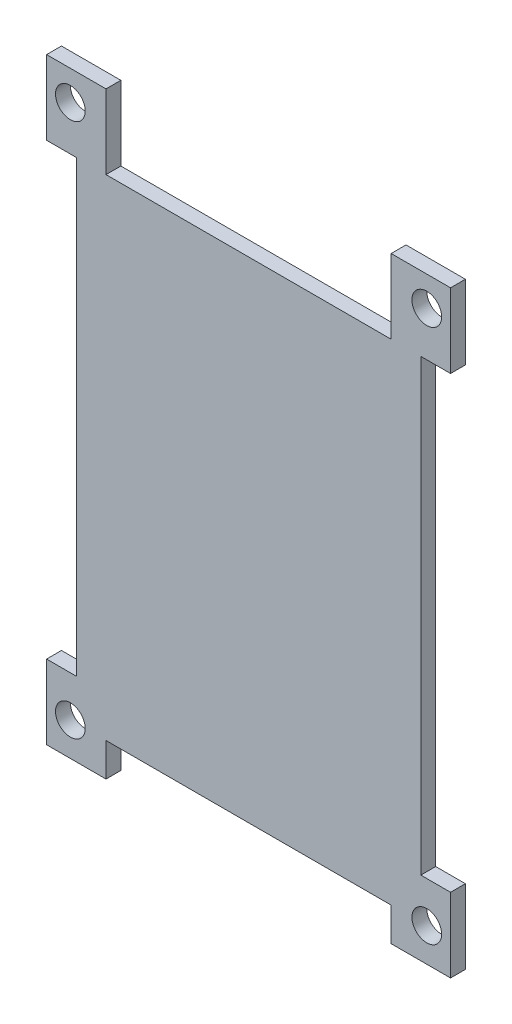
SolidWorks part; units mm, degrees
material "PVC 0.007 plastifié"
ref_plane "Face" through (0, 0, 0) normal (0, 0, 1) x (1, 0, 0)
ref_plane "Dessus" through (0, 0, 0) normal (0, 1, 0) x (1, 0, 0)
ref_plane "Droite" through (0, 0, 0) normal (1, 0, 0) x (0, 0, -1)
sketch "Esquisse1" plane through (0, 0, 0) normal (0, 0, 1) x (1, 0, 0)
  line L0 (0, 0) -> (33.0541, 0) construction
  line L1 (-19.2, 33) -> (19.2, 33)
  line L2 (-23.2, 33) -> (-23.2, -27.5)
  line L3 (19.2, -33) -> (-19.2, -33)
  line L4 (23.2, 33) -> (23.2, -27.5)
  line L5 (0, 0) -> (0, 31.1956) construction
  line L6 (19.2, 43) -> (19.2, 33)
  line L7 (-27.2, 43) -> (-19.2, 43)
  line L8 (-27.2, 43) -> (-27.2, 33)
  line L9 (-27.2, 33) -> (-23.2, 33)
  line L10 (-19.2, 43) -> (-19.2, 33)
  line L11 (19.2, -37.5) -> (27.2, -37.5)
  line L12 (27.2, 43) -> (27.2, 33)
  line L13 (27.2, 43) -> (19.2, 43)
  line L14 (27.2, -37.5) -> (27.2, -27.5)
  line L15 (27.2, -27.5) -> (23.2, -27.5)
  line L16 (-19.2, -37.5) -> (-27.2, -37.5)
  line L17 (-19.2, -37.5) -> (-19.2, -33)
  line L18 (-27.2, -37.5) -> (-27.2, -27.5)
  line L21 (19.2, -37.5) -> (19.2, -33)
  line L22 (-27.2, -27.5) -> (-23.2, -27.5)
  line L23 (23.2, 33) -> (27.2, 33)
  dimension "D1" = 46.4
  dimension "D2" = 66
  dimension "D3" = 8
  dimension "D4" = 4
  dimension "D5" = 10
  dimension "D6" = 4.5
  dimension "D7" = 10
  dimension "D8" = 8
  dimension "D9" = 8
  dimension "D10" = 4
  dimension "D11" = 27.5
extrude "Extrusion1" add sketch "Esquisse1" along normal blind 2
sketch "Esquisse2" plane through (0, 0, 2) normal (0, 0, 1) x (1, 0, 0)
  line L0 (0, 0) -> (0, 28.1312) construction
  line L3 (0, 0) -> (33.3419, 0) construction
  line L5 (-19.2, 43) -> (-27.2, 43) construction
  circle A0 centre (-24, 39) radius 2
  circle A1 centre (24, 39) radius 2
  circle A2 centre (-24, -33) radius 2
  circle A3 centre (24, -33) radius 2
  dimension "D1" = 24
  dimension "D4" = 72
  dimension "D2" = 4
  dimension "D5" = 4
  dimension "D6" = 4
  dimension "D3" = 4
extrude "Enlèv. mat.-Extru.1" cut sketch "Esquisse2" against normal through all
